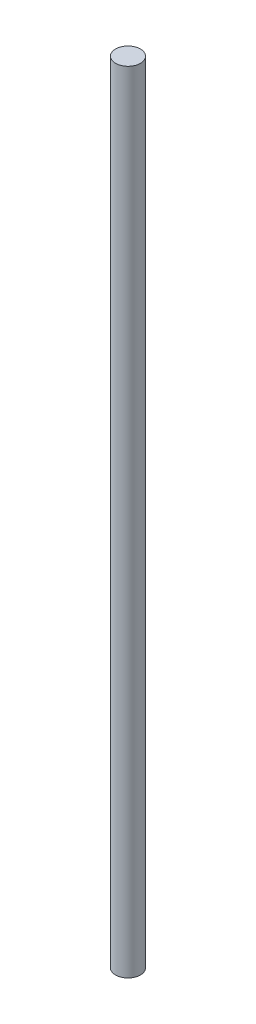
SolidWorks part; units mm, degrees
ref_plane "Front Plane" through (0, 0, 0) normal (0, 0, 1) x (1, 0, 0)
ref_plane "Top Plane" through (0, 0, 0) normal (0, 1, 0) x (1, 0, 0)
ref_plane "Right Plane" through (0, 0, 0) normal (1, 0, 0) x (0, 0, -1)
sketch "Sketch1" plane through (0, 0, 0) normal (0, 1, 0) x (1, 0, 0)
  circle A0 centre (0, 0) radius 4
  dimension "D1" = 8
extrude "Boss-Extrude1" add sketch "Sketch1" along normal blind 254
